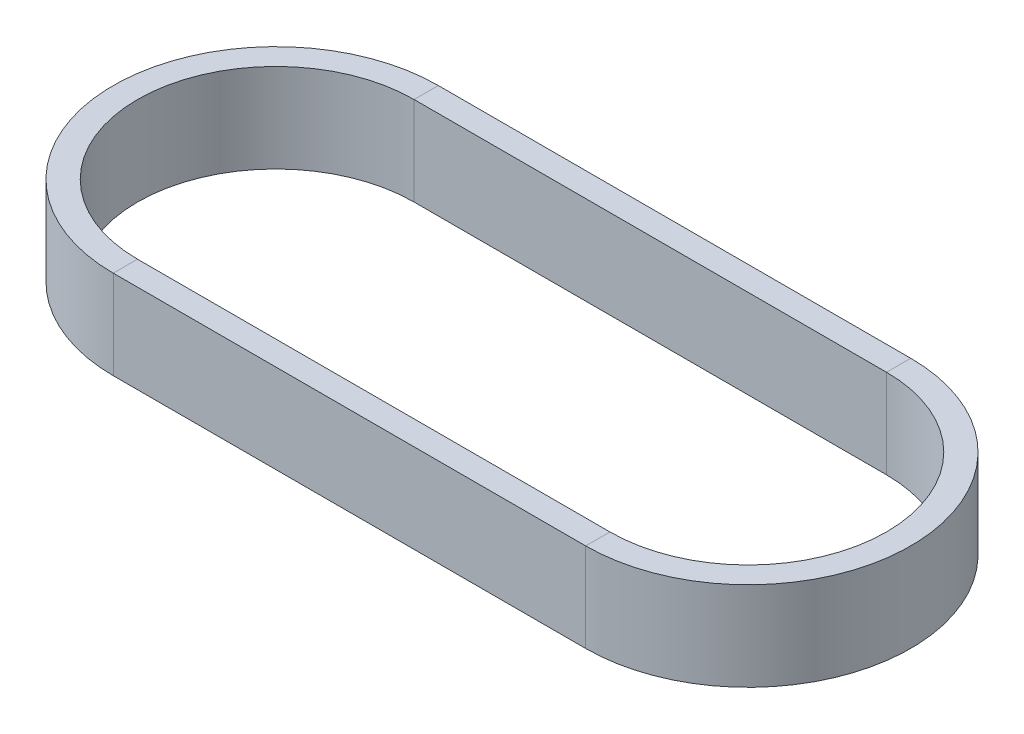
SolidWorks part; units mm, degrees
ref_plane "Front Plane" through (0, 0, 0) normal (0, 0, 1) x (1, 0, 0)
ref_plane "Top Plane" through (0, 0, 0) normal (0, 1, 0) x (1, 0, 0)
ref_plane "Right Plane" through (0, 0, 0) normal (1, 0, 0) x (0, 0, -1)
sketch "Sketch1" plane through (0, 0, 0) normal (0, 1, 0) x (1, 0, 0)
  line L0 (0, 0) -> (-117.0056, 0) construction
  line L1 (0, -37.2489) -> (-117.0056, -37.2489)
  line L2 (0, 37.2489) -> (-117.0056, 37.2489)
  arc A0 (0, -37.2489) -> (0, 37.2489) centre (0, 0) ccw
  arc A1 (-117.0056, 37.2489) -> (-117.0056, -37.2489) centre (-117.0056, 0) ccw
  point P3 (-58.5028, 0)
  dimension "D2" = 37.2489
  dimension "D1" = 117.0056
ref_plane "Plane1" through (-117.0056, 0, 37.2489) normal (-1, 0, 0) x (0, 0, 1)
sketch "Sketch2" plane through (-117.0056, 0, 37.2489) normal (-1, 0, 0) x (0, 0, 1)
  line L1 (-3, 11) -> (3, 11)
  line L2 (-3, 11) -> (-3, -11)
  line L3 (-3, -11) -> (3, -11)
  line L4 (3, 11) -> (3, -11)
  line L5 (-3, 11) -> (3, -11) construction
  line L6 (-3, -11) -> (3, 11) construction
  point P0 (0, 0)
  dimension "D1" = 22
  dimension "D2" = 6
sweep "Sweep1" add profiles "Sketch2" path "Sketch1"
